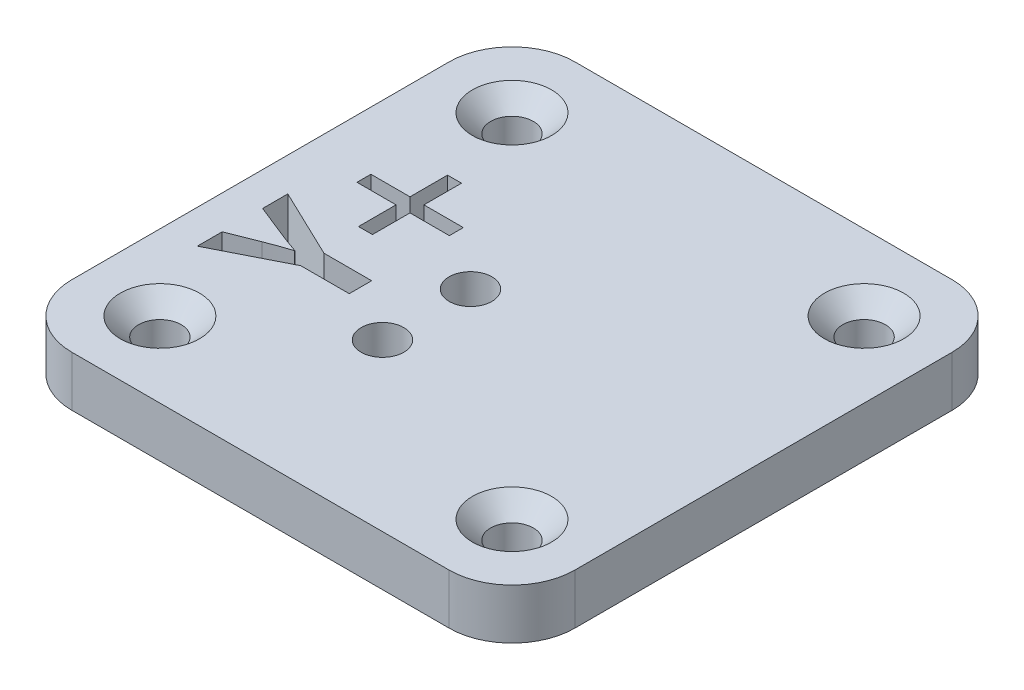
SolidWorks part; units mm, degrees
ref_plane "Front Plane" through (0, 0, 0) normal (0, 0, 1) x (1, 0, 0)
ref_plane "Top Plane" through (0, 0, 0) normal (0, 1, 0) x (1, 0, 0)
ref_plane "Right Plane" through (0, 0, 0) normal (1, 0, 0) x (0, 0, -1)
sketch "Sketch1" plane through (0, 0, 0) normal (0, 1, 0) x (1, 0, 0)
  line L1 (-15, -20) -> (15, -20)
  line L2 (-20, -15) -> (-20, 15)
  line L3 (-15, 20) -> (15, 20)
  line L4 (20, -15) -> (20, 15)
  line L5 (-20, -20) -> (20, 20) construction
  line L6 (-20, 20) -> (20, -20) construction
  arc A0 (20, -15) -> (15, -20) centre (15, -15) cw
  arc A1 (-15, -20) -> (-20, -15) centre (-15, -15) cw
  arc A2 (20, 15) -> (15, 20) centre (15, 15) ccw
  arc A3 (-15, 20) -> (-20, 15) centre (-15, 15) ccw
  point P0 (0, 0)
  dimension "D3" = 5
  dimension "D1" = 40
  dimension "D2" = 40
extrude "Boss-Extrude1" add sketch "Sketch1" along normal blind 4
sketch "Sketch2" plane through (0, 4, 0) normal (0, 1, 0) x (1, 0, 0)
  line L1 (-14, -14) -> (14, -14) construction
  line L2 (-14, -14) -> (-14, 14) construction
  line L3 (-14, 14) -> (14, 14) construction
  line L4 (14, -14) -> (14, 14) construction
  line L5 (-14, -14) -> (14, 14) construction
  line L6 (-14, 14) -> (14, -14) construction
  point P0 (0, 0)
  dimension "D1" = 28
  dimension "D2" = 28
hole_wizard "CSK for M3 Countersunk Flat Head Screw1" positions "3DSketch1" profile "Sketch3" countersink size "M3" standard "DIN" end condition through all
sketch3d "3DSketch1"
  point P0 (-14, 4, -14)
  point P3 (14, 4, -14)
  point P6 (14, 4, 14)
  point P9 (-14, 4, 14)
sketch "Sketch3" plane through (-14, 4, -14) normal (1, 0, 0) x (0, 0, 1)
  line L0 (0, 0) -> (0, 4)
  line L1 (0, 4) -> (1.7, 4)
  line L2 (1.7, 4) -> (1.7, 1.45)
  line L3 (1.7, 1.45) -> (3.15, 0)
  line L5 (3.15, 0) -> (0, 0)
  line L6 (-1.7, 1.45) -> (-3.15, 0) construction
  line L11 (0, -6.35) -> (0, 107.95) construction
  dimension "Thru Hole Dia." = 3.4
  dimension "Thru Hole Depth" = 4
  dimension "Near C'Sink Dia." = 6.3
  dimension "Near C'Sink Angle" = 90
sketch "Sketch4" plane through (0, 0, 0) normal (0, 1, 0) x (1, 0, 0)
  arc A0 (-5.25, 0.2) -> (-1.75, 0.2) centre (-3.5, 0.2) ccw construction
  arc A1 (-1.75, 0.2) -> (-5.25, 0.2) centre (-3.5, 0.2) ccw construction
  arc A2 (-5.25, -6.8) -> (-1.75, -6.8) centre (-3.5, -6.8) ccw construction
  arc A3 (-1.75, -6.8) -> (-5.25, -6.8) centre (-3.5, -6.8) ccw construction
  arc A4 (-5.25, 0.2) -> (-1.75, 0.2) centre (-3.5, 0.2) ccw construction
  arc A5 (-1.75, 0.2) -> (-5.25, 0.2) centre (-3.5, 0.2) ccw construction
  arc A6 (-5.25, -6.8) -> (-1.75, -6.8) centre (-3.5, -6.8) ccw construction
  arc A7 (-1.75, -6.8) -> (-5.25, -6.8) centre (-3.5, -6.8) ccw construction
hole_wizard "CSK for M3 Countersunk Flat Head Screw2" positions "Sketch5" profile "Sketch6" countersink size "M3" standard "DIN" end condition through all
sketch "Sketch5" plane through (0, 0, 0) normal (0, -1, 0) x (-1, 0, 0)
  point P0 (3.5, 0.2)
  point P3 (3.5, -6.8)
sketch "Sketch6" plane through (-3.5, 0, -0.2) normal (1, 0, 0) x (0, 0, -1)
  line L0 (0, 0) -> (0, 4)
  line L1 (0, 4) -> (1.7, 4)
  line L2 (1.7, 4) -> (1.7, 1.45)
  line L3 (1.7, 1.45) -> (3.15, 0)
  line L5 (3.15, 0) -> (0, 0)
  line L6 (-1.7, 1.45) -> (-3.15, 0) construction
  line L11 (0, -6.35) -> (0, 107.95) construction
  dimension "Thru Hole Dia." = 3.4
  dimension "Thru Hole Depth" = 4
  dimension "Near C'Sink Dia." = 6.3
  dimension "Near C'Sink Angle" = 90
sketch "Sketch7" plane through (0, 4, 0) normal (0, 1, 0) x (1, 0, 0)
  line L0 (-8, 20) -> (-8, -20) construction
  line L1 (15, 20) -> (-15, 20) construction
  line L2 (0, 0) -> (0, 20) construction
  line L3 (-15, -20) -> (15, -20) construction
  text T0 "+Y" font "@Adobe Gothic Std B" height in points 30
  dimension "D2" = 8
extrude "Cut-Extrude1" cut sketch "Sketch7" against normal up to surface (4 mm away) up to face at (-3.5, 0, -3.35)
